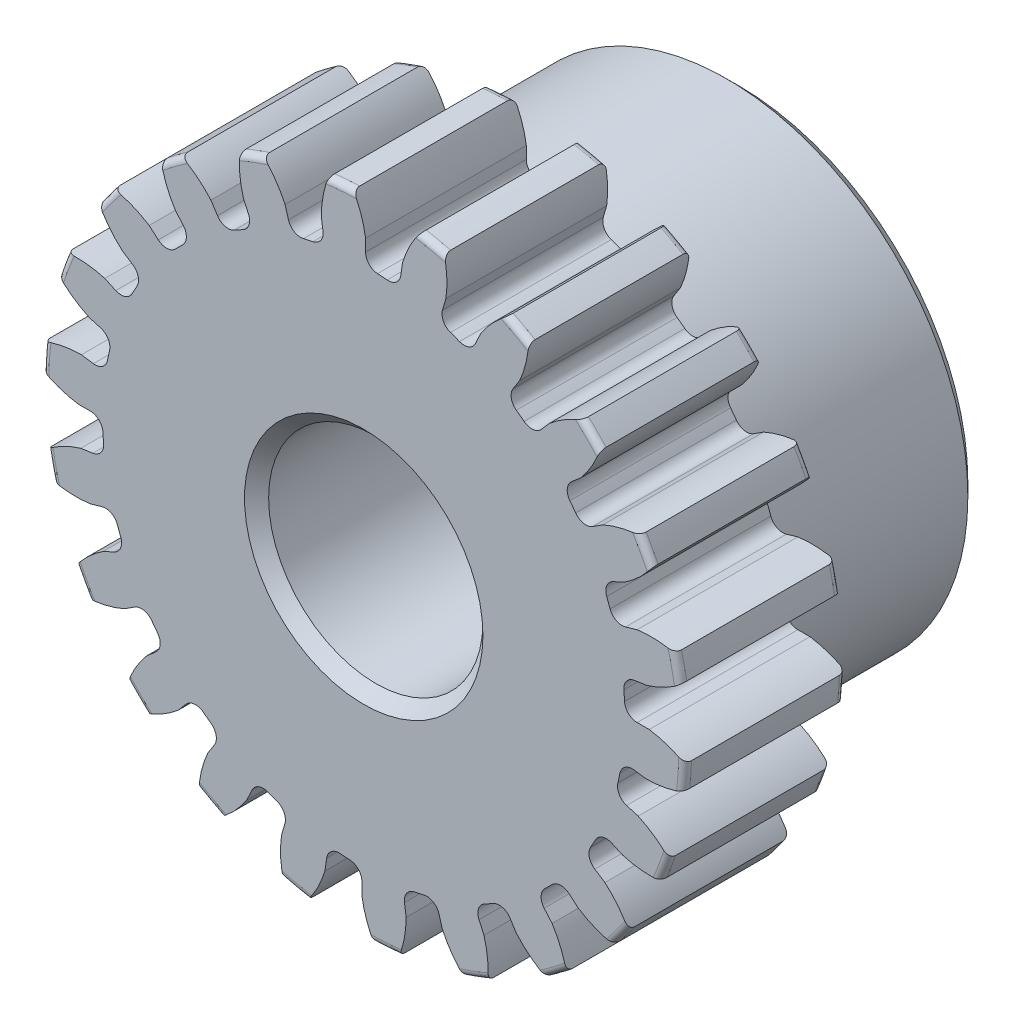
SolidWorks part; units mm, degrees
ref_plane "Front" through (0, 0, 0) normal (0, 0, 1) x (1, 0, 0)
ref_plane "Top" through (0, 0, 0) normal (0, 1, 0) x (1, 0, 0)
ref_plane "Right" through (0, 0, 0) normal (1, 0, 0) x (0, 0, -1)
sketch "Sketch1" plane through (0, 0, 0) normal (0, 0, 1) x (1, 0, 0)
  line L0 (-279.4, 0) -> (279.4, 0) construction
  circle A0 centre (0, 0) radius 9.525
  circle A1 centre (0, 0) radius 8.7376 construction
  circle A3 centre (0, 0) radius 7.7378 construction
  dimension "D3" = 0.7874
  dimension "D1" = 1.7872
extrude "Boss-Extrude1" add sketch "Sketch1" against normal blind 4.7625
sketch "Sketch2" plane through (0, 0, 0) normal (1, 0, 0) x (0, 0, -1)
  line L0 (4.7625, 0) -> (11.1125, 0)
  line L1 (4.7625, 0) -> (4.7625, 7.1438)
  line L2 (4.7625, 7.1438) -> (11.1125, 7.1437)
  line L3 (11.1125, 7.1437) -> (11.1125, 0)
  point P5 (11.1125, -7.1437)
  point P6 (0, -9.525)
  point P7 (4.7625, -9.525)
  point P9 (0, 9.525)
revolve "Revolve1" add sketch "Sketch2" angle 360 mid plane about L0
fillet "Fillet2" radius 0.1905 3 edges at (9.525, 0, -4.7625) (9.525, 0, 0) (7.1438, 0, -4.7625)
sketch "Sketch3" plane through (0, 0, 0) normal (0, 0, 1) x (1, 0, 0)
  line L0 (0, 0) -> (0, 9.525) construction
  line L1 (-2.118, 8.1898) -> (0, 8.7376)
  line L2 (-9.5921, 8.7376) -> (9.5921, 8.7376) construction
  line L3 (-9.2865, 6.3359) -> (9.2865, 11.1393) construction
  line L4 (-2.118, 8.1898) -> (0, 0) construction
  line L5 (-5.4024, 6.5095) -> (0, 0) construction
  line L6 (-5.4024, 6.5095) -> (-0.8766, 10.2656) construction
  line L7 (-1.4769, 8.3294) -> (0, 0) construction
  line L8 (-1.4769, 8.3294) -> (0.031, 8.5967) construction
  arc A0 (-2.118, 8.1898) -> (-5.4024, 6.5095) centre (0, 0) ccw
  circle A1 centre (0, 0) radius 8.7376 construction
  circle A2 centre (0, 0) radius 8.4593 construction
  arc A3 (-2.118, 8.1898) -> (-1.4769, 8.3294) centre (0, 0) cw
  circle A4 centre (0, 0) radius 9.525 construction
  point P6 (0, 8.7376)
  dimension "D1" = 2.1877
  dimension "D3" = 5.8814
  dimension "D5" = 1.5314
  dimension "D2" = 3.7191
  dimension "D4" = 0.6563
sketch "Sketch4" plane through (0, 0, 0) normal (0, 0, 1) x (1, 0, 0)
  line L0 (0, 0) -> (0.6217, 8.6931) construction
  line L1 (0.0548, 8.4591) -> (0.0548, 7.7376)
  line L2 (0, 8.7376) -> (1.2435, 8.6487) construction
  line L3 (1.1496, 8.3808) -> (1.0469, 7.6666)
  line L4 (0.0548, 7.7376) -> (0, 0) construction
  line L5 (0, 0) -> (0, 9.525) construction
  line L6 (-5.4024, 6.5095) -> (-0.8766, 10.2656) construction
  line L7 (-5.4024, 6.5095) -> (-0.8766, 10.2656) construction
  arc A0 (1.0469, 7.6666) -> (0.0548, 7.7376) centre (0, 0) ccw
  arc A1 (0, 8.7376) -> (1.2435, 8.6487) centre (0, 0) cw construction
  circle A2 centre (0, 0) radius 8.7376 construction
  circle A3 centre (0, 0) radius 8.4593 construction
  circle A4 centre (0, 0) radius 7.7378 construction
  arc A5 (2.3286, 10.0364) -> (-0.8766, 10.2656) centre (0, 0) ccw
  spline S0 degree 2 poles (-0.8766, 10.2656) (-0.0977, 9.4713) (0.0548, 8.4591) knots 0 0 0 1 1 1
  spline S1 degree 2 poles (2.3286, 10.0364) (1.4446, 9.361) (1.1496, 8.3808) knots 0 0 0 1 1 1
  dimension "D1" = 1.2477
extrude "Cut-Extrude1" cut sketch "Sketch4" against normal through all
fillet "Fillet1" radius 0.3743 2 edges at (1.0469, 7.6666, -2.3813) (0.0548, 7.7376, -2.3813)
pattern_circular "CirPattern1" count 22 over 360 about axis through (0, 0, -4.7625) along (0, 0, 1) of "Cut-Extrude1", "Fillet1"
sketch "Sketch5" plane through (0, 0, 0) normal (0, 0, 1) x (1, 0, 0)
  circle A0 centre (0, 0) radius 3.175
  circle A1 centre (0, 0) radius 1.5875 construction
  dimension "Bore Min" = 6.35
  dimension "Bore Max" = 3.175
extrude "Cut-Extrude2" cut sketch "Sketch5" against normal through all
chamfer "Chamfer1" distance 0.3572 angle 45 3 edges at (7.1437, 0, -11.1125) (3.175, 0, 0) (3.175, 0, -11.1125)
sketch "Pitch Dia" plane through (0, 0, 0) normal (0, 0, 1) x (1, 0, 0)
  circle A0 centre (0, 0) radius 8.7376 construction
  circle A1 centre (0, 0) radius 8.7376 construction
equation "\"D1@Boss-Extrude1\" = \"Face Wd@Sketch2\""
equation "\"D2@Sketch3\" = \"D1@Sketch3\"*1.7"
equation "\"D3@Sketch3\" = \"D1@Sketch3\"+\"D2@Sketch3\"-.001"
equation "\"D4@Sketch3\" = \"D1@Sketch3\"*.3"
equation "\"D5@Sketch3\" = \"D1@Sketch3\"-\"D4@Sketch3\""
equation "\"D1@Sketch4\" = 1.5708/(\"Number of Teeth@Sketch1\"/\"Ptich Dia@Sketch1\")"
equation "\"D1@Chamfer1\" = \"B Hub Dia@Sketch2\"*.025"
equation "\"D1@CirPattern1\" = \"Number of Teeth@Sketch1\""
equation "\"D1@Fillet1\" = \"D1@Sketch4\"*.3"
equation "\"D1@Fillet2\" = \"OD@Sketch1\"*.01"
equation "\"D1@Sketch1\" = 2.250/(\"Number of Teeth@Sketch1\"/\"Ptich Dia@Sketch1\")"
